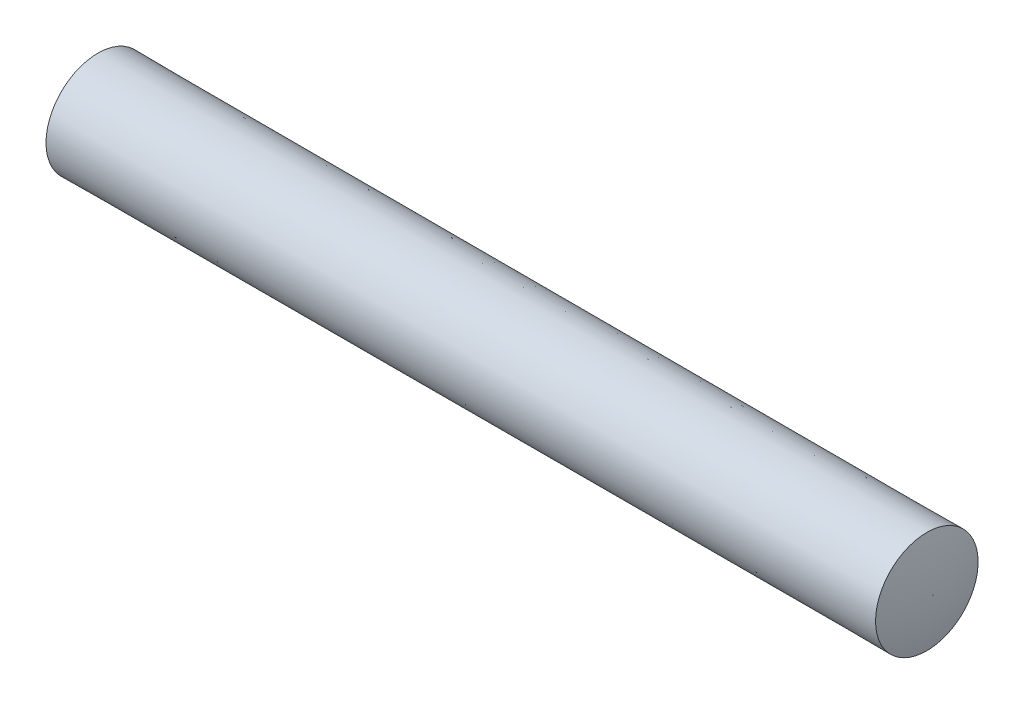
SolidWorks part; units mm, degrees
ref_plane "Plane1" through (0, 0, 0) normal (0, 0, 1) x (1, 0, 0)
ref_plane "Plane2" through (0, 0, 0) normal (0, 1, 0) x (1, 0, 0)
ref_plane "Plane3" through (0, 0, 0) normal (1, 0, 0) x (0, 0, -1)
sketch "Sketch1" plane through (0, 0, 0) normal (0, 0, 1) x (1, 0, 0)
  line L1 (-5.588, 0) -> (131.826, 0) construction
  line L2 (0, 0) -> (0, 0.0079)
  line L3 (0, 0) -> (12.8955, 0)
  line L4 (12.8955, 0) -> (12.8955, 0.0079)
  line L5 (12.7988, 0.7855) -> (0.0988, 0.7937)
  arc A0 (0, 0.0079) -> (0.0988, 0.7937) centre (3.175, 0.0079) cw
  arc A1 (12.8955, 0.0079) -> (12.7988, 0.7855) centre (9.7205, 0.0079) ccw
  dimension "D3" = 3.175
  dimension "D4" = 3.175
  dimension "D1" = 0.0079
  dimension "D2" = 0.0079
  dimension "Length" = 12.7
  dimension "Diameter" = 1.5875
  dimension "D5" = 1.571
revolve "Base-Revolve" add sketch "Sketch1" angle 360 about L1
equation "\"D1@Sketch1\" = \"Diameter@Sketch1\" / 100 / 2"
equation "\"D2@Sketch1\" = \"Diameter@Sketch1\" / 100 / 2"
equation "\"D3@Sketch1\" = \"Diameter@Sketch1\" *2"
equation "\"D4@Sketch1\" = \"Diameter@Sketch1\" *2"
equation "\"D5@Sketch1\" = \"Diameter@Sketch1\" -  (\"Length@Sketch1\" * (1/48) * \"Diameter@Sketch1\")"
